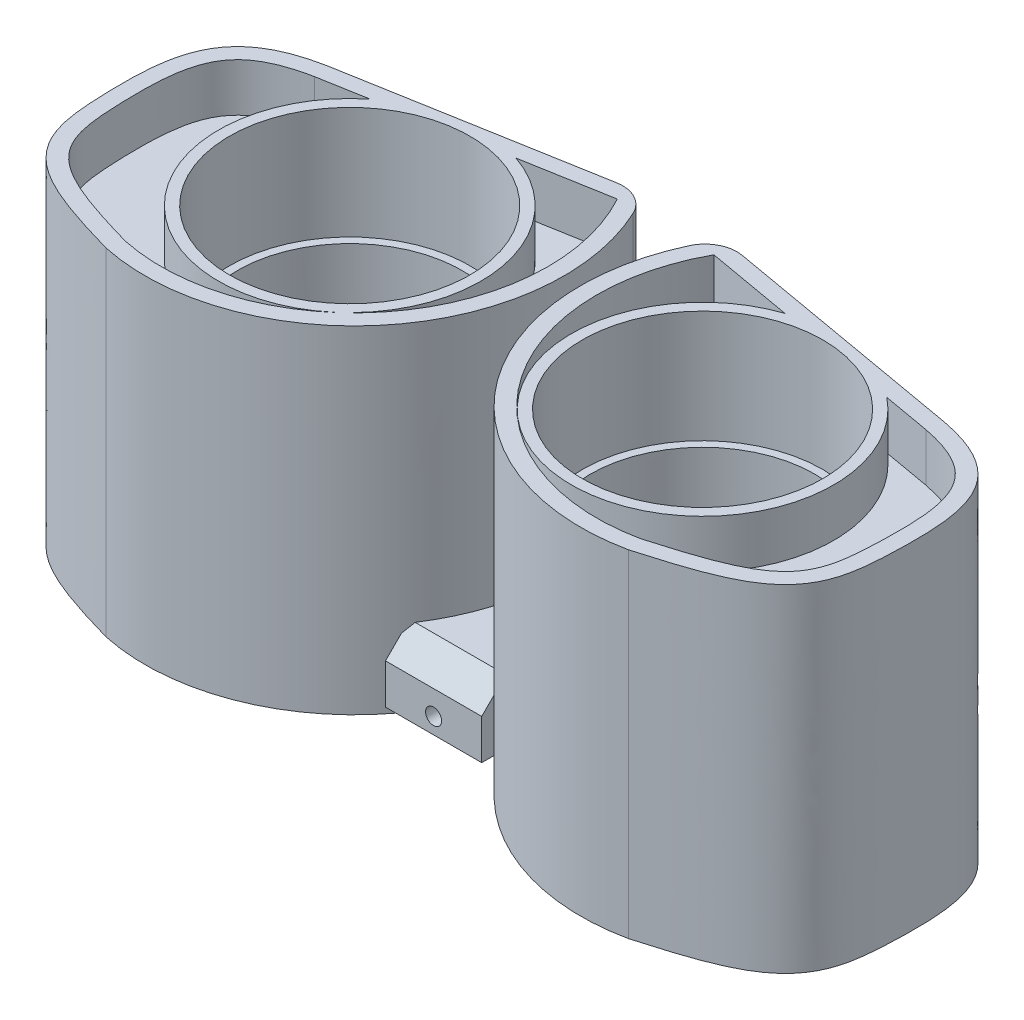
SolidWorks part; units mm, degrees
ref_plane "Front" through (0, 0, 0) normal (0, 0, 1) x (1, 0, 0)
ref_plane "Top" through (0, 0, 0) normal (0, 1, 0) x (1, 0, 0)
ref_plane "Right" through (0, 0, 0) normal (1, 0, 0) x (0, 0, -1)
sketch "草图1" plane through (0, 0, 0) normal (0, 1, 0) x (1, 0, 0)
  line L0 (-19.1474, 0) -> (24.6079, 0) construction
  line L1 (0, 18.5446) -> (0, -20.1047) construction
  line L2 (2.5, 0) -> (19.2417, -2.952)
  line L3 (19.2417, -2.952) -> (16.2897, -19.6938) construction
  line L4 (17.6789, -11.8153) -> (24.5726, -13.0308) construction
  line L5 (-2.5, 0) -> (-19.2417, -2.952)
  arc A0 (16.2897, -19.6938) -> (2.5, 0) centre (13.5849, -6.913) cw
  arc A1 (-16.2897, -19.6938) -> (-2.5, 0) centre (-13.5849, -6.913) ccw
  spline S0 degree 3 poles (16.2897, -19.6938) (21.1298, -18.3094) (24.3655, -17.0369) (24.9303, -7.3751) (24.2805, -3.9218) (19.2417, -2.952) knots 0 0 0 0 0.384247 0.484247 1 1 1 1
  spline S1 degree 3 poles (-16.2897, -19.6938) (-21.1298, -18.3094) (-24.3655, -17.0369) (-24.9303, -7.3751) (-24.2805, -3.9218) (-19.2417, -2.952) knots 0 0 0 0 0.384247 0.484247 1 1 1 1
  dimension "D1" = 17
  dimension "D2" = 17
  dimension "D3" = 10
  dimension "D4" = 2.5
  dimension "D5" = 8
  dimension "D6" = 7
extrude "凸台-拉伸1" add sketch "草图1" along normal blind 21
ref_plane "左右对称面" through (0, 0, 0) normal (1, 0, 0) x (0, 0, -1)
sketch "草图9" plane through (0, 21, 0) normal (0, 1, 0) x (1, 0, 0)
  line L2 (-3.0109, -1.1055) -> (-19.0603, -3.9354)
  line L3 (-3.0109, -1.1055) -> (-19.0603, -3.9354)
  arc A2 (-16.049, -18.7225) -> (-3.0109, -1.1055) centre (-13.5849, -6.913) ccw
  arc A3 (-16.049, -18.7225) -> (-3.0109, -1.1055) centre (-13.5849, -6.913) ccw
  spline S2 degree 3 poles (-858.3784, 2875.3912) (77.3924, -123.0861) (6.4969, 4.6727) (-20.5938, -4.3446) (-20.8058, -4.425) (-21.2222, -4.6095) (-21.4276, -4.7144) (-21.8172, -4.9505) (-22.0024, -5.082) (-22.3485, -5.3788) (-22.5099, -5.5456) (-22.7913, -5.9017) (-22.9135, -6.0922) (-23.1246, -6.496) (-23.2133, -6.7093) (-23.4325, -7.3549) (-23.5216, -7.7998) (-23.6408, -8.705) (-23.6695, -9.1594) (-23.6958, -10.0676) (-23.693, -10.522) (-23.672, -11.431) (-23.6562, -11.8863) (-23.5969, -12.7933) (-23.5538, -13.2451) (-23.4303, -13.9154) (-23.3778, -14.1388) (-23.2417, -14.5746) (-23.159, -14.7857) (-22.9575, -15.1915) (-22.8374, -15.3879) (-22.5628, -15.7536) (-22.4102, -15.9213) (-22.0797, -16.2315) (-21.9008, -16.3748) (-21.5278, -16.6384) (-21.3354, -16.7579) (-20.7458, -17.0912) (-20.3368, -17.2802) (-19.5026, -17.6247) (-19.0767, -17.78) (21.5473, -31.5912) (86.418, 34.1995) (-785.5463, -2916.626) knots -3.84625 -3.84625 -3.84625 -3.84625 0.0625 0.0625 0.09375 0.09375 0.125 0.125 0.15625 0.15625 0.1875 0.1875 0.21875 0.21875 0.25 0.25 0.3125 0.3125 0.375 0.375 0.4375 0.4375 0.5 0.5 0.5625 0.5625 0.59375 0.59375 0.625 0.625 0.65625 0.65625 0.6875 0.6875 0.71875 0.71875 0.75 0.75 0.8125 0.8125 0.875 0.875 6.730352 6.730352 6.730352 6.730352 only from (-19.0603, -3.9354) to (-16.049, -18.7225)
  spline S3 degree 3 poles (-19.0603, -3.9354) (-19.5082, -4.0219) (-19.9492, -4.13) (-20.5938, -4.3446) (-20.8058, -4.425) (-21.2222, -4.6095) (-21.4276, -4.7144) (-21.8172, -4.9505) (-22.0024, -5.082) (-22.3485, -5.3788) (-22.5099, -5.5456) (-22.7913, -5.9017) (-22.9135, -6.0922) (-23.1246, -6.496) (-23.2133, -6.7093) (-23.4325, -7.3549) (-23.5216, -7.7998) (-23.6408, -8.705) (-23.6695, -9.1594) (-23.6958, -10.0676) (-23.693, -10.522) (-23.672, -11.431) (-23.6562, -11.8863) (-23.5969, -12.7933) (-23.5538, -13.2451) (-23.4303, -13.9154) (-23.3778, -14.1388) (-23.2417, -14.5746) (-23.159, -14.7857) (-22.9575, -15.1915) (-22.8374, -15.3879) (-22.5628, -15.7536) (-22.4102, -15.9213) (-22.0797, -16.2315) (-21.9008, -16.3748) (-21.5278, -16.6384) (-21.3354, -16.7579) (-20.7458, -17.0912) (-20.3368, -17.2802) (-19.5026, -17.6247) (-19.0767, -17.78) (-17.7896, -18.2175) (-16.9202, -18.4731) (-16.049, -18.7225) knots 0 0 0 0 0.0625 0.0625 0.09375 0.09375 0.125 0.125 0.15625 0.15625 0.1875 0.1875 0.21875 0.21875 0.25 0.25 0.3125 0.3125 0.375 0.375 0.4375 0.4375 0.5 0.5 0.5625 0.5625 0.59375 0.59375 0.625 0.625 0.65625 0.65625 0.6875 0.6875 0.71875 0.71875 0.75 0.75 0.8125 0.8125 0.875 0.875 1 1 1 1
  dimension "D1" = 1
extrude "切除-拉伸5" cut sketch "草图9" against normal blind 3
sketch "草图10" plane through (0, 21, 0) normal (0, 1, 0) x (1, 0, 0)
  line L2 (19.0603, -3.9354) -> (3.0109, -1.1055)
  line L3 (19.0603, -3.9354) -> (3.0109, -1.1055)
  arc A2 (3.0109, -1.1055) -> (16.049, -18.7225) centre (13.5849, -6.913) ccw
  arc A3 (3.0109, -1.1055) -> (16.049, -18.7225) centre (13.5849, -6.913) ccw
  spline S2 degree 3 poles (791.3663, -2915.1113) (-86.5838, 34.1407) (-21.552, -31.5917) (19.0759, -17.7802) (19.5021, -17.6249) (20.3362, -17.2805) (20.7448, -17.0917) (21.3331, -16.7593) (21.525, -16.6401) (21.8967, -16.3779) (22.0773, -16.2336) (22.4084, -15.9232) (22.5603, -15.7562) (22.8326, -15.3949) (22.9539, -15.1982) (23.2601, -14.5834) (23.3872, -14.1475) (23.5539, -13.2462) (23.5969, -12.793) (23.6562, -11.8872) (23.6719, -11.4338) (23.693, -10.5269) (23.6958, -10.0731) (23.6698, -9.1648) (23.641, -8.7079) (23.5224, -7.8043) (23.4335, -7.3577) (23.2123, -6.7065) (23.1248, -6.4966) (22.9148, -6.0946) (22.7913, -5.9013) (22.5067, -5.5418) (22.3487, -5.3792) (22.0051, -5.0842) (21.8181, -4.951) (21.2317, -4.5956) (20.8151, -4.4186) (-5.185, 4.2554) (-80.5888, -109.1263) (2091.1107, 2165.3633) knots -5.732806 -5.732806 -5.732806 -5.732806 0.125 0.125 0.1875 0.1875 0.25 0.25 0.28125 0.28125 0.3125 0.3125 0.34375 0.34375 0.375 0.375 0.4375 0.4375 0.5 0.5 0.5625 0.5625 0.625 0.625 0.6875 0.6875 0.75 0.75 0.78125 0.78125 0.8125 0.8125 0.84375 0.84375 0.875 0.875 0.9375 0.9375 4.646734 4.646734 4.646734 4.646734 only from (16.049, -18.7225) to (19.0603, -3.9354)
  spline S3 degree 3 poles (16.049, -18.7225) (16.92, -18.4731) (17.7891, -18.2177) (19.0759, -17.7802) (19.5021, -17.6249) (20.3362, -17.2805) (20.7448, -17.0917) (21.3331, -16.7593) (21.525, -16.6401) (21.8967, -16.3779) (22.0773, -16.2336) (22.4084, -15.9232) (22.5603, -15.7562) (22.8326, -15.3949) (22.9539, -15.1982) (23.2601, -14.5834) (23.3872, -14.1475) (23.5539, -13.2462) (23.5969, -12.793) (23.6562, -11.8872) (23.6719, -11.4338) (23.693, -10.5269) (23.6958, -10.0731) (23.6698, -9.1648) (23.641, -8.7079) (23.5224, -7.8043) (23.4335, -7.3577) (23.2123, -6.7065) (23.1248, -6.4966) (22.9148, -6.0946) (22.7913, -5.9013) (22.5067, -5.5418) (22.3487, -5.3792) (22.0051, -5.0842) (21.8181, -4.951) (21.2317, -4.5956) (20.8151, -4.4186) (19.9534, -4.1311) (19.5084, -4.022) (19.0603, -3.9354) knots 0 0 0 0 0.125 0.125 0.1875 0.1875 0.25 0.25 0.28125 0.28125 0.3125 0.3125 0.34375 0.34375 0.375 0.375 0.4375 0.4375 0.5 0.5 0.5625 0.5625 0.625 0.625 0.6875 0.6875 0.75 0.75 0.78125 0.78125 0.8125 0.8125 0.84375 0.84375 0.875 0.875 0.9375 0.9375 1 1 1 1
  dimension "D1" = 1
extrude "切除-拉伸6" cut sketch "草图10" against normal blind 3
sketch "草图2" plane through (0, 21, 0) normal (0, 1, 0) x (1, 0, 0)
  line L0 (0, 0) -> (47.9111, 0) construction
  line L1 (11, 17.6245) -> (11, -32.1256) construction
  line L2 (0, 18.4114) -> (0, -32.3256) construction
  circle A0 centre (11, -9.8) radius 7
  circle A1 centre (-11, -9.8) radius 7
  dimension "D1" = 14
  dimension "D2" = 9.8
  dimension "D3" = 22
extrude "镜头" cut sketch "草图2" against normal through all
fillet "圆角1" radius 2 1 edges at (-2.5, 10.5, 0)
fillet "圆角2" radius 2 1 edges at (2.5, 10.5, 0)
sketch "草图6" plane through (0, 0, 0) normal (0, 1, 0) x (1, 0, 0)
  line L0 (0, 8.4586) -> (0, -23.7271) construction
  line L2 (3, -10) -> (-3, -10)
  line L3 (3, -10) -> (3, -2)
  line L4 (3, -2) -> (-3, -2)
  line L5 (-3, -10) -> (-3, -2)
  line L6 (3, -10) -> (-3, -2) construction
  line L7 (3, -2) -> (-3, -10) construction
  point P3 (0, -6)
  dimension "D1" = 6
  dimension "D2" = 8
  dimension "D3" = 6
extrude "凸台-拉伸2" add sketch "草图6" along normal blind 8
sketch "草图11" plane through (0, 0, 0) normal (0, -1, 0) x (1, 0, 0)
  line L4 (1.5362, 9.2) -> (-1.5362, 9.2)
  line L9 (-19.0966, 3.7388) -> (-3.7746, 1.0371)
  line L10 (-2.0313, 2.8) -> (2.0313, 2.8)
  line L11 (3.7746, 1.0371) -> (19.0966, 3.7388)
  line L13 (-19.0966, 3.7388) -> (-3.7746, 1.0371)
  line L14 (-2.0313, 2.8) -> (2.0313, 2.8)
  line L15 (3.7746, 1.0371) -> (19.0966, 3.7388)
  line L19 (1.5362, 9.2) -> (-1.5362, 9.2)
  arc A12 (-1.5362, 9.2) -> (-16.097, 18.9168) centre (-13.5849, 6.913) ccw
  arc A13 (-3.7746, 1.0371) -> (-2.4796, 1.7097) centre (-3.5662, 2.2189) ccw
  arc A14 (-2.4796, 1.7097) -> (-2.0313, 2.8) centre (-13.5849, 6.913) ccw
  arc A15 (2.0313, 2.8) -> (2.4796, 1.7097) centre (13.5849, 6.913) ccw
  arc A16 (2.4796, 1.7097) -> (3.7746, 1.0371) centre (3.5662, 2.2189) ccw
  arc A17 (16.097, 18.9168) -> (1.5362, 9.2) centre (13.5849, 6.913) ccw
  arc A18 (-1.5362, 9.2) -> (-16.097, 18.9168) centre (-13.5849, 6.913) ccw
  arc A19 (-3.7746, 1.0371) -> (-2.4796, 1.7097) centre (-3.5662, 2.2189) ccw
  arc A20 (-2.4796, 1.7097) -> (-2.0313, 2.8) centre (-13.5849, 6.913) ccw
  arc A21 (2.0313, 2.8) -> (2.4796, 1.7097) centre (13.5849, 6.913) ccw
  arc A22 (2.4796, 1.7097) -> (3.7746, 1.0371) centre (3.5662, 2.2189) ccw
  arc A23 (16.097, 18.9168) -> (1.5362, 9.2) centre (13.5849, 6.913) ccw
  spline S4 degree 3 poles (-794.8928, 2914.3039) (87.0191, -35.11) (21.458, 31.8423) (-19.1949, 17.9502) (-19.631, 17.79) (-20.483, 17.4339) (-20.8998, 17.2382) (-21.4981, 16.893) (-21.6929, 16.7692) (-22.0697, 16.4968) (-22.2532, 16.3464) (-22.5894, 16.0231) (-22.7431, 15.8497) (-23.0182, 15.4764) (-23.1404, 15.275) (-23.4518, 14.6416) (-23.582, 14.1943) (-23.7527, 13.2709) (-23.7968, 12.8051) (-23.8571, 11.8751) (-23.873, 11.4097) (-23.8936, 10.4783) (-23.8957, 10.0124) (-23.8656, 9.0793) (-23.8336, 8.6106) (-23.7366, 7.9171) (-23.696, 7.6873) (-23.5919, 7.2315) (-23.5279, 7.0045) (-23.3712, 6.5651) (-23.2784, 6.352) (-23.0564, 5.9426) (-22.9252, 5.7443) (-22.6316, 5.3824) (-22.4691, 5.2175) (-22.1156, 4.917) (-21.9228, 4.7804) (-21.3228, 4.4175) (-20.8961, 4.2352) (5.8083, -4.6983) (81.0436, 113.2312) (-1968.7973, -2275.9501) knots -5.602575 -5.602575 -5.602575 -5.602575 0.125 0.125 0.1875 0.1875 0.25 0.25 0.28125 0.28125 0.3125 0.3125 0.34375 0.34375 0.375 0.375 0.4375 0.4375 0.5 0.5 0.5625 0.5625 0.625 0.625 0.6875 0.6875 0.71875 0.71875 0.75 0.75 0.78125 0.78125 0.8125 0.8125 0.84375 0.84375 0.875 0.875 0.9375 0.9375 4.650437 4.650437 4.650437 4.650437 only from (-16.097, 18.9168) to (-19.0966, 3.7388)
  spline S5 degree 3 poles (866.0449, -2873.2773) (-79.7566, 125.104) (-6.9756, -5.0634) (20.6675, 4.1585) (20.8846, 4.241) (21.3109, 4.4301) (21.5214, 4.5377) (21.9212, 4.7793) (22.1113, 4.9137) (22.4672, 5.2155) (22.6341, 5.3851) (22.9274, 5.7473) (23.0554, 5.9409) (23.2776, 6.3504) (23.3723, 6.5678) (23.607, 7.2272) (23.7035, 7.6818) (23.8332, 8.6067) (23.8653, 9.0738) (23.8956, 10.0049) (23.8937, 10.4706) (23.8732, 11.4025) (23.8573, 11.8692) (23.7973, 12.7993) (23.7534, 13.2625) (23.5857, 14.1784) (23.4538, 14.6339) (23.1487, 15.2598) (23.0282, 15.4613) (22.751, 15.8405) (22.5971, 16.0148) (22.0962, 16.4991) (21.7077, 16.7714) (20.9062, 17.2351) (20.4883, 17.4315) (19.6353, 17.7884) (19.1995, 17.9486) (-21.4386, 31.8418) (-86.7191, -35.2819) (784.5347, 2917.0712) knots -3.832138 -3.832138 -3.832138 -3.832138 0.0625 0.0625 0.09375 0.09375 0.125 0.125 0.15625 0.15625 0.1875 0.1875 0.21875 0.21875 0.25 0.25 0.3125 0.3125 0.375 0.375 0.4375 0.4375 0.5 0.5 0.5625 0.5625 0.625 0.625 0.65625 0.65625 0.6875 0.6875 0.75 0.75 0.8125 0.8125 0.875 0.875 6.591545 6.591545 6.591545 6.591545 only from (19.0966, 3.7388) to (16.097, 18.9168)
  spline S6 degree 3 poles (-16.097, 18.9168) (-16.9887, 18.6615) (-17.8784, 18.4001) (-19.1949, 17.9502) (-19.631, 17.79) (-20.483, 17.4339) (-20.8998, 17.2382) (-21.4981, 16.893) (-21.6929, 16.7692) (-22.0697, 16.4968) (-22.2532, 16.3464) (-22.5894, 16.0231) (-22.7431, 15.8497) (-23.0182, 15.4764) (-23.1404, 15.275) (-23.4518, 14.6416) (-23.582, 14.1943) (-23.7527, 13.2709) (-23.7968, 12.8051) (-23.8571, 11.8751) (-23.873, 11.4097) (-23.8936, 10.4783) (-23.8957, 10.0124) (-23.8656, 9.0793) (-23.8336, 8.6106) (-23.7366, 7.9171) (-23.696, 7.6873) (-23.5919, 7.2315) (-23.5279, 7.0045) (-23.3712, 6.5651) (-23.2784, 6.352) (-23.0564, 5.9426) (-22.9252, 5.7443) (-22.6316, 5.3824) (-22.4691, 5.2175) (-22.1156, 4.917) (-21.9228, 4.7804) (-21.3228, 4.4175) (-20.8961, 4.2352) (-20.012, 3.9394) (-19.556, 3.8274) (-19.0966, 3.7388) knots 0 0 0 0 0.125 0.125 0.1875 0.1875 0.25 0.25 0.28125 0.28125 0.3125 0.3125 0.34375 0.34375 0.375 0.375 0.4375 0.4375 0.5 0.5 0.5625 0.5625 0.625 0.625 0.6875 0.6875 0.71875 0.71875 0.75 0.75 0.78125 0.78125 0.8125 0.8125 0.84375 0.84375 0.875 0.875 0.9375 0.9375 1 1 1 1
  spline S7 degree 3 poles (19.0966, 3.7388) (19.5556, 3.8273) (20.0074, 3.9383) (20.6675, 4.1585) (20.8846, 4.241) (21.3109, 4.4301) (21.5214, 4.5377) (21.9212, 4.7793) (22.1113, 4.9137) (22.4672, 5.2155) (22.6341, 5.3851) (22.9274, 5.7473) (23.0554, 5.9409) (23.2776, 6.3504) (23.3723, 6.5678) (23.607, 7.2272) (23.7035, 7.6818) (23.8332, 8.6067) (23.8653, 9.0738) (23.8956, 10.0049) (23.8937, 10.4706) (23.8732, 11.4025) (23.8573, 11.8692) (23.7973, 12.7993) (23.7534, 13.2625) (23.5857, 14.1784) (23.4538, 14.6339) (23.1487, 15.2598) (23.0282, 15.4613) (22.751, 15.8405) (22.5971, 16.0148) (22.0962, 16.4991) (21.7077, 16.7714) (20.9062, 17.2351) (20.4883, 17.4315) (19.6353, 17.7884) (19.1995, 17.9486) (17.881, 18.3993) (16.99, 18.6612) (16.097, 18.9168) knots 0 0 0 0 0.0625 0.0625 0.09375 0.09375 0.125 0.125 0.15625 0.15625 0.1875 0.1875 0.21875 0.21875 0.25 0.25 0.3125 0.3125 0.375 0.375 0.4375 0.4375 0.5 0.5 0.5625 0.5625 0.625 0.625 0.65625 0.65625 0.6875 0.6875 0.75 0.75 0.8125 0.8125 0.875 0.875 1 1 1 1
  dimension "D1" = 0.8
extrude "切除-拉伸7" cut sketch "草图11" against normal blind 3.5
sketch "草图12" plane through (0, 3.5, 0) normal (0, -1, 0) x (1, 0, 0)
  line L0 (0, -19.0387) -> (0, 28.4339) construction
  line L1 (11, 9.8) -> (-38.793, 9.8) construction
  line L2 (-5, 3.8) -> (-17, 3.8)
  line L7 (5, 15.8) -> (17, 15.8)
  line L8 (5, 15.8) -> (5, 3.8)
  line L9 (5, 3.8) -> (17, 3.8)
  line L10 (17, 15.8) -> (17, 3.8)
  line L11 (5, 15.8) -> (17, 3.8) construction
  line L12 (5, 3.8) -> (17, 15.8) construction
  line L13 (-17, 15.8) -> (-17, 3.8)
  line L14 (-5, 15.8) -> (-17, 15.8)
  line L15 (-5, 15.8) -> (-5, 3.8)
  dimension "D1" = 12
  dimension "D2" = 12
extrude "切除-拉伸8" cut sketch "草图12" against normal blind 3.5 and the other way through all
sketch "草图13" plane through (0, 3.5, 0) normal (0, -1, 0) x (1, 0, 0)
  line L0 (0, -17.2689) -> (0, 27.9362) construction
  line L1 (47.281, 10) -> (-45.8309, 10) construction
  circle A0 centre (22.5, 10) radius 0.5
  circle A1 centre (-22.5, 10) radius 0.5
  dimension "D2" = 1
  dimension "D1" = 10
  dimension "D3" = 45
extrude "切除-拉伸9" cut sketch "草图13" against normal blind 5
sketch "草图14" plane through (0, 18, 0) normal (0, 1, 0) x (1, 0, 0)
  line L0 (-3.9135, -0.2492) -> (-19.2417, -2.952) construction
  line L1 (0, 11.0372) -> (0, -22.7434) construction
  circle A1 centre (-11, -9.8) radius 8.1751
  circle A2 centre (-11, -9.8) radius 7.5
  circle A3 centre (11, -9.8) radius 7.5
  circle A4 centre (11, -9.8) radius 8.1751
  dimension "D1" = 15
extrude "凸台-拉伸3" add sketch "草图14" along normal blind 3
sketch "草图15" plane through (0, 21, 0) normal (0, 1, 0) x (1, 0, 0)
  line L0 (0, 8.274) -> (0, -21.1642) construction
  circle A0 centre (-11, -9.8) radius 7.5
  circle A1 centre (11, -9.8) radius 7.5
  dimension "D1" = 15
extrude "切除-拉伸10" cut sketch "草图15" against normal blind 7
sketch "草图16" plane through (0, 0, 10) normal (0, 0, 1) x (1, 0, 0)
  line L0 (0, 24.5968) -> (0, -6.7896) construction
  line L1 (-0.891, 0) -> (0.891, 0) construction
  line L2 (4, 0) -> (-4, 0)
  line L3 (4, 0) -> (4, 4)
  line L4 (4, 4) -> (-4, 4)
  line L5 (-4, 0) -> (-4, 4)
  line L6 (4, 0) -> (-4, 4) construction
  line L7 (4, 4) -> (-4, 0) construction
  point P3 (0, 2)
  point P10 (4, 2)
  dimension "D1" = 4
  dimension "D2" = 8
extrude "凸台-拉伸4" [suppressed] add sketch "草图16" along normal blind 5
ref_plane "基准面1" through (0, 0.8, 0) normal (0, -1, 0) x (-1, 0, 0)
sketch "草图18" plane through (0, 0.8, 0) normal (0, -1, 0) x (1, 0, 0)
  line L0 (-0.891, 10) -> (-3, 14.5696)
  line L1 (-0.891, 10) -> (0.891, 10)
  line L7 (-3, 14.5696) -> (4.0311, 14.5696) construction
  line L8 (0.891, 10) -> (3, 14.5696)
  line L9 (3, 14.5696) -> (3, 15.5696)
  line L10 (3, 15.5696) -> (-3, 15.5696)
  line L11 (-3, 15.5696) -> (-3, 14.5696)
  arc A2 (-0.891, 10) -> (-16.2897, 19.6938) centre (-13.5849, 6.913) ccw construction
  arc A3 (16.2897, 19.6938) -> (0.891, 10) centre (13.5849, 6.913) ccw construction
  dimension "D1" = 6
  dimension "D2" = 1
extrude "凸台-拉伸5" add sketch "草图18" against normal blind 4
sketch "草图19" plane through (0, 0, 15.5696) normal (0, 0, 1) x (1, 0, 0)
  line L0 (0, 25.8058) -> (0, -6.6629) construction
  circle A0 centre (0, 1.8) radius 0.5
  dimension "D1" = 1
  dimension "D2" = 1.8
extrude "切除-拉伸11" cut sketch "草图19" against normal blind 4
chamfer "倒角1" distance 1.5 angle 45 1 edges at (0, 4.8, 15.5696)
chamfer "倒角2" distance 1 angle 45 1 edges at (0, 8, 10)
